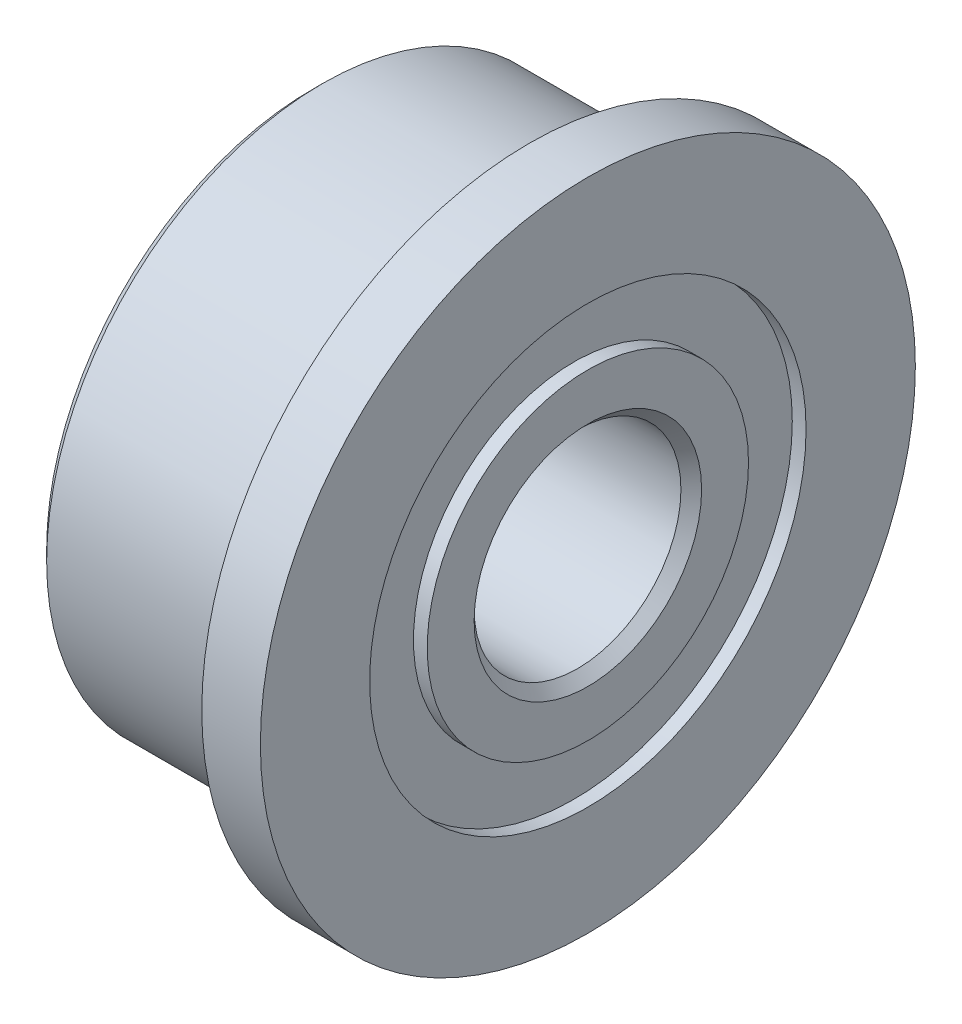
SolidWorks part; units mm, degrees
material "Alloy Steel"
ref_plane "Front Plane" through (0, 0, 0) normal (0, 0, 1) x (1, 0, 0)
ref_plane "Top Plane" through (0, 0, 0) normal (0, 1, 0) x (1, 0, 0)
ref_plane "Right Plane" through (0, 0, 0) normal (1, 0, 0) x (0, 0, -1)
sketch "Sketch1" plane through (0, 0, 0) normal (0, 0, 1) x (1, 0, 0)
  line L0 (0, 0) -> (-4, 0) construction
  line L1 (55, 0) -> (-55, 0) construction
  line L2 (-4, 1.5) -> (0, 1.5)
  line L3 (0, 1.5) -> (0, 2.33)
  line L4 (0, 4.75) -> (-0.85, 4.75)
  line L5 (-0.85, 4.75) -> (-0.85, 4.02)
  line L6 (-0.87, 4) -> (-4, 4)
  line L7 (-4, 4) -> (-4, 3.165)
  line L8 (0, -55) -> (0, 55) construction
  line L9 (-4, 2.33) -> (-4, 1.5)
  line L10 (-4, 3.165) -> (-3.8, 3.165)
  line L11 (0, 3.165) -> (0, 4.75)
  line L12 (-4, 2.33) -> (-3.8, 2.33)
  line L13 (-3.8, 3.165) -> (-3.8, 2.33)
  line L14 (-0.2, 3.165) -> (0, 3.165)
  line L15 (-0.2, 3.165) -> (-0.2, 2.33)
  line L16 (-0.2, 2.33) -> (0, 2.33)
  arc A0 (-0.87, 4) -> (-0.85, 4.02) centre (-0.85, 4) ccw
  dimension "D6" = 0.02
  dimension "D1" = 3
  dimension "D2" = 8
  dimension "D3" = 9.5
  dimension "D4" = 0.85
  dimension "D5" = 4
  dimension "D7" = 4.66
  dimension "D8" = 6.33
  dimension "D9" = 0.2
revolve "Revolve1" add sketch "Sketch1" angle 360 about L0
chamfer "Chamfer1" distance 0.15 angle 45 3 edges at (0, 0, -1.5) (-4, 0, -1.5) (-4, 0, -4)
